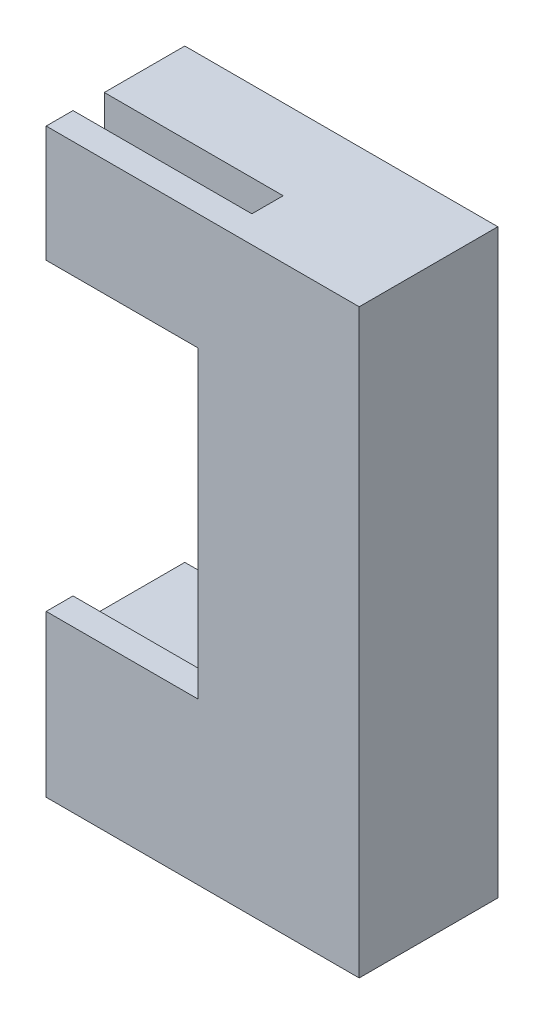
SolidWorks part; units mm, degrees
material "PVC 0.007 Plasticized"
ref_plane "Front Plane" through (0, 0, 0) normal (0, 0, 1) x (1, 0, 0)
ref_plane "Top Plane" through (0, 0, 0) normal (0, 1, 0) x (1, 0, 0)
ref_plane "Right Plane" through (0, 0, 0) normal (1, 0, 0) x (0, 0, -1)
sketch "Sketch1" plane through (0, 0, 0) normal (0, 0, 1) x (1, 0, 0)
  line L0 (0, 0) -> (0, 65)
  line L1 (0, 65) -> (-35, 65)
  line L2 (-35, 65) -> (-35, 55)
  line L3 (-35, 55) -> (-15, 55)
  line L4 (-15, 55) -> (-15, 15)
  line L5 (-15, 15) -> (-35, 15)
  line L6 (-35, 15) -> (-35, 0)
  line L7 (-35, 0) -> (0, 0)
  dimension "D1" = 65
  dimension "D2" = 35
  dimension "D3" = 15
  dimension "D4" = 20
  dimension "D5" = 15
  dimension "D6" = 40
extrude "Boss-Extrude1" add sketch "Sketch1" along normal blind 12.5
ref_plane "Plane1" through (0, 65, 0) normal (0, 1, 0) x (1, 0, 0)
sketch "Sketch2" plane through (0, 65, 0) normal (0, 1, 0) x (1, 0, 0)
  line L0 (-35, -12.5) -> (-35, 0) construction
  line L1 (-35, -9) -> (-15, -9)
  line L2 (-35, -9) -> (-35, -12.5)
  line L3 (-35, -12.5) -> (-15, -12.5)
  line L4 (-15, -9) -> (-15, -12.5)
  line L5 (0, -12.5) -> (-35, -12.5) construction
  dimension "D1" = 20
  dimension "D2" = 3.5
extrude "Cut-Extrude1" cut sketch "Sketch2" against normal blind 10
ref_plane "Plane2" through (0, 0, 12.5) normal (0, 0, 1) x (1, 0, 0)
sketch "Sketch3" plane through (0, 0, 12.5) normal (0, 0, 1) x (1, 0, 0)
  line L0 (-35, 0) -> (0, 0)
  line L1 (0, 0) -> (0, 65)
  line L2 (6.875, 65) -> (-6.875, 65) construction
  line L3 (0, 0) -> (0, 65) construction
  line L4 (0, 65) -> (-35, 65)
  line L5 (-35, 65) -> (-35, 52)
  line L6 (-35, 52) -> (-18, 52)
  line L7 (-18, 52) -> (-18, 18)
  line L8 (-18, 18) -> (-35, 18)
  line L9 (-35, 18) -> (-35, 0)
  line L10 (-15, 55) -> (-35, 55) construction
  line L11 (-15, 65) -> (-15, 15) construction
  line L12 (-15, 15) -> (-35, 15) construction
  dimension "D1" = 3
  dimension "D2" = 3
  dimension "D3" = 3
  dimension "D4" = 35
extrude "Boss-Extrude2" add sketch "Sketch3" along normal blind 3
ref_plane "Plane3" through (-35, 0, 0) normal (-1, 0, 0) x (0, 0, 1)
sketch "Sketch4" plane through (-35, 0, 0) normal (-1, 0, 0) x (0, 0, 1)
  line L0 (0, 15) -> (0, 0) construction
  line L1 (12.5, 15) -> (0, 15) construction
  circle A0 centre (5, 10) radius 2.5
  dimension "D3" = 5
  dimension "D1" = 5
  dimension "D2" = 5
extrude "Cut-Extrude2" cut sketch "Sketch4" against normal blind 5
ref_plane "Plane4" through (-15, 0, 0) normal (-1, 0, 0) x (0, 0, 1)
sketch "Sketch5" plane through (-15, 0, 0) normal (-1, 0, 0) x (0, 0, 1)
  line L0 (0, 55) -> (0, 15) construction
  line L1 (0, 18.9) -> (4, 18.9)
  line L2 (0, 18.9) -> (0, 16.7)
  line L3 (0, 16.7) -> (4, 16.7)
  line L4 (4, 18.9) -> (4, 16.7)
  line L5 (9, 55) -> (0, 55) construction
  line L6 (0, 53.3) -> (4, 53.3)
  line L7 (0, 53.3) -> (0, 51.1)
  line L8 (0, 51.1) -> (4, 51.1)
  line L9 (4, 53.3) -> (4, 51.1)
  line L10 (12.5, 15) -> (0, 15) construction
  dimension "D1" = 4
  dimension "D2" = 2.2
  dimension "D3" = 1.7
  dimension "D4" = 1.7
  dimension "D5" = 2.2
  dimension "D6" = 4
extrude "Boss-Extrude3" add sketch "Sketch5" along normal blind 4
